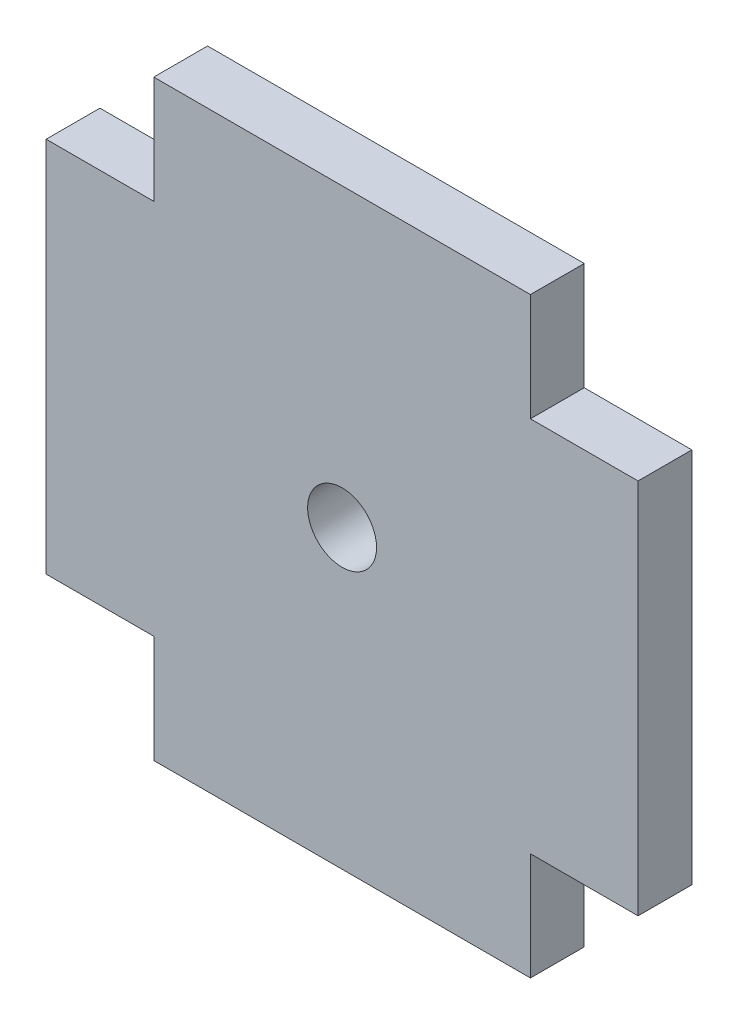
SolidWorks part; units mm, degrees
ref_plane "Front Plane" through (0, 0, 0) normal (0, 0, 1) x (1, 0, 0)
ref_plane "Top Plane" through (0, 0, 0) normal (0, 1, 0) x (1, 0, 0)
ref_plane "Right Plane" through (0, 0, 0) normal (1, 0, 0) x (0, 0, -1)
sketch "Sketch1" plane through (0, 0, 0) normal (0, 0, 1) x (1, 0, 0)
  line L0 (-17.5, 27.5) -> (-17.5, 17.5) construction
  line L1 (-17.5, 27.5) -> (17.5, 27.5)
  line L2 (-27.5, 17.5) -> (-27.5, -17.5)
  line L3 (-17.5, -27.5) -> (17.5, -27.5)
  line L4 (27.5, 17.5) -> (27.5, -17.5)
  line L5 (-17.5, 17.5) -> (-27.5, 17.5) construction
  line L6 (17.5, 27.5) -> (17.5, 17.5) construction
  line L7 (17.5, 17.5) -> (27.5, 17.5) construction
  line L8 (17.5, -27.5) -> (17.5, -17.5) construction
  line L9 (17.5, -17.5) -> (27.5, -17.5) construction
  line L10 (-17.5, -27.5) -> (-17.5, -17.5) construction
  line L11 (-17.5, -17.5) -> (-27.5, -17.5) construction
  line L12 (-27.5, 17.5) -> (-17.5, 17.5)
  line L17 (-17.5, 17.5) -> (-17.5, 27.5)
  line L18 (17.5, 27.5) -> (17.5, 17.5)
  line L19 (17.5, 17.5) -> (27.5, 17.5)
  line L20 (27.5, -17.5) -> (17.5, -17.5)
  line L21 (17.5, -17.5) -> (17.5, -27.5)
  line L22 (-17.5, -27.5) -> (-17.5, -17.5)
  line L23 (-17.5, -17.5) -> (-27.5, -17.5)
  circle A0 centre (0, 0) radius 3.2
  dimension "D2" = 6.4
  dimension "D3" = 27.5
  dimension "D4" = 27.5
  dimension "D5" = 10
  dimension "D6" = 10
  dimension "D7" = 10
  dimension "D8" = 10
  dimension "D9" = 10
  dimension "D10" = 10
  dimension "D11" = 10
  dimension "D12" = 10
extrude "Boss-Extrude1" add sketch "Sketch1" against normal blind 5
